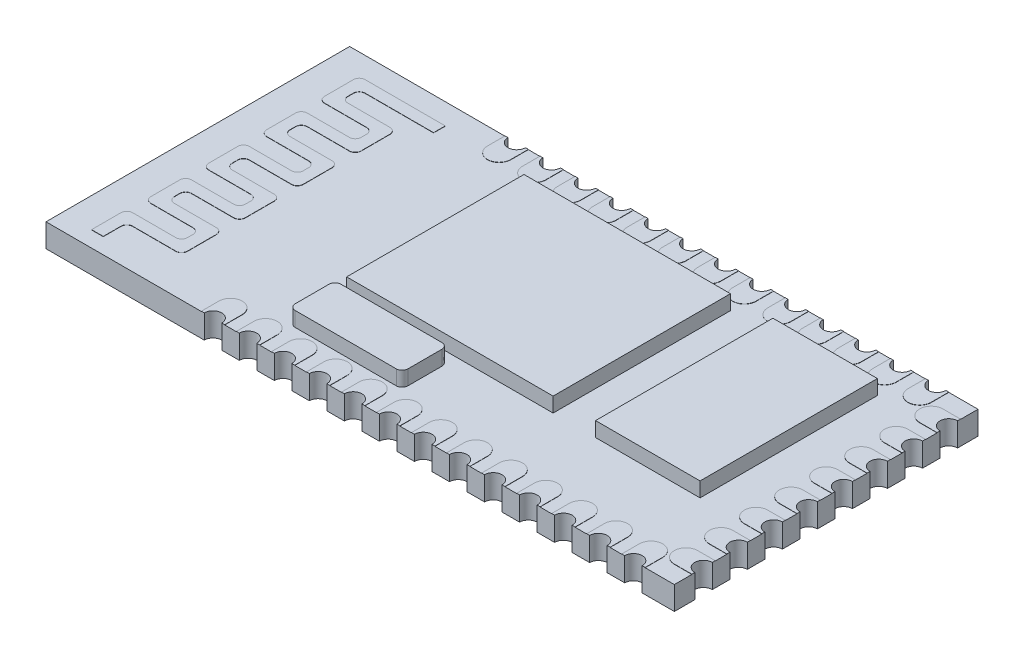
SolidWorks part; units mm, degrees
ref_plane "Front Plane" through (0, 0, 0) normal (0, 0, 1) x (1, 0, 0)
ref_plane "Top Plane" through (0, 0, 0) normal (0, 1, 0) x (1, 0, 0)
ref_plane "Right Plane" through (0, 0, 0) normal (1, 0, 0) x (0, 0, -1)
sketch "Sketch1" plane through (0, 0, 0) normal (0, 1, 0) x (1, 0, 0)
  line L1 (0, 0) -> (26.9, 0)
  line L2 (0, 0) -> (0, 13)
  line L3 (0, 13) -> (26.9, 13)
  line L4 (26.9, 0) -> (26.9, 13)
  dimension "D1" = 13
  dimension "D2" = 26.9
extrude "Boss-Extrude1" add sketch "Sketch1" along normal blind 1
sketch "Sketch2" plane through (0, 1, 0) normal (0, 1, 0) x (1, 0, 0)
  line L1 (24.2376, 11.3557) -> (19.7636, 11.3557)
  line L2 (24.2376, 11.3557) -> (24.2376, 3.7634)
  line L3 (24.2376, 3.7634) -> (19.7636, 3.7634)
  line L4 (19.7636, 11.3557) -> (19.7636, 3.7634)
  line L5 (9.1073, 11.3557) -> (17.9469, 11.3557)
  line L6 (9.1073, 11.3557) -> (9.1073, 3.7634)
  line L7 (9.1073, 3.7634) -> (17.9469, 3.7634)
  line L8 (17.9469, 11.3557) -> (17.9469, 3.7634)
extrude "Boss-Extrude2" add sketch "Sketch2" along normal blind 0.63
sketch "Sketch3" plane through (0, 1, 0) normal (0, 1, 0) x (1, 0, 0)
  line L0 (5.0017, 11.8414) -> (1.5699, 11.8414) construction
  line L1 (1.5699, 11.8414) -> (1.5699, 10.6027) construction
  line L2 (1.5699, 10.6027) -> (3.8747, 10.6027) construction
  line L3 (3.8747, 10.6027) -> (3.8747, 9.364) construction
  line L4 (3.8747, 9.364) -> (1.5699, 9.364) construction
  line L5 (1.5699, 9.364) -> (1.5699, 8.1252) construction
  line L6 (1.5699, 8.1252) -> (3.8747, 8.1252) construction
  line L7 (3.8747, 8.1252) -> (3.8747, 6.8865) construction
  line L8 (3.8747, 6.8865) -> (1.5699, 6.8865) construction
  line L9 (1.5699, 6.8865) -> (1.5699, 5.6478) construction
  line L10 (1.5699, 5.6478) -> (3.8747, 5.6478) construction
  line L11 (3.8747, 5.6478) -> (3.8747, 4.4091) construction
  line L12 (3.8747, 4.4091) -> (1.5699, 4.4091) construction
  line L13 (1.5699, 4.4091) -> (1.5699, 3.1704) construction
  line L14 (1.5699, 3.1704) -> (3.8747, 3.1704) construction
  line L15 (3.8747, 3.1704) -> (3.8747, 1.9317) construction
  line L16 (3.8747, 1.9317) -> (1.527, 1.9317) construction
  line L17 (1.527, 1.4451) -> (1.527, 0.1872) construction
  line L18 (5.0017, 12.0914) -> (1.5699, 12.0914)
  line L19 (1.3199, 11.8414) -> (1.3199, 10.6027)
  line L20 (1.5699, 10.3527) -> (3.3747, 10.3527)
  line L21 (3.6247, 10.1027) -> (3.6247, 9.864)
  line L22 (3.3747, 9.614) -> (1.5699, 9.614)
  line L23 (1.3199, 9.364) -> (1.3199, 8.1252)
  line L24 (1.5699, 7.8752) -> (3.3747, 7.8752)
  line L25 (3.6247, 7.6252) -> (3.6247, 7.3865)
  line L26 (3.3747, 7.1365) -> (1.5699, 7.1365)
  line L27 (1.3199, 6.8865) -> (1.3199, 5.6478)
  line L28 (1.5699, 5.3978) -> (3.3747, 5.3978)
  line L29 (3.6247, 5.1478) -> (3.6247, 4.9091)
  line L30 (3.3747, 4.6591) -> (1.5699, 4.6591)
  line L31 (1.3199, 4.4091) -> (1.3199, 3.1704)
  line L32 (1.5699, 2.9204) -> (3.3747, 2.9204)
  line L33 (3.6247, 2.6704) -> (3.6247, 2.4317)
  line L34 (3.3747, 2.1817) -> (1.527, 2.1817)
  line L35 (1.277, 1.9317) -> (1.277, 0.6739)
  line L36 (5.0017, 11.5914) -> (2.0699, 11.5914)
  line L37 (1.8199, 11.3414) -> (1.8199, 11.1027)
  line L38 (2.0699, 10.8527) -> (3.8747, 10.8527)
  line L39 (4.1247, 10.6027) -> (4.1247, 9.364)
  line L40 (3.8747, 9.114) -> (2.0699, 9.114)
  line L41 (1.8199, 8.864) -> (1.8199, 8.6252)
  line L42 (2.0699, 8.3752) -> (3.8747, 8.3752)
  line L43 (4.1247, 8.1252) -> (4.1247, 6.8865)
  line L44 (3.8747, 6.6365) -> (2.0699, 6.6365)
  line L45 (1.8199, 6.3865) -> (1.8199, 6.1478)
  line L46 (2.0699, 5.8978) -> (3.8747, 5.8978)
  line L47 (4.1247, 5.6478) -> (4.1247, 4.4091)
  line L48 (3.8747, 4.1591) -> (2.0699, 4.1591)
  line L49 (1.8199, 3.9091) -> (1.8199, 3.6704)
  line L50 (2.0699, 3.4204) -> (3.8747, 3.4204)
  line L51 (4.1247, 3.1704) -> (4.1247, 1.9317)
  line L52 (3.8747, 1.6817) -> (2.027, 1.6817)
  line L53 (1.777, 1.4317) -> (1.777, 0.6739)
  line L54 (5.0017, 12.0914) -> (5.0017, 11.5914)
  line L55 (1.777, 0.6739) -> (1.277, 0.6739)
  arc A0 (1.5699, 12.0914) -> (1.3199, 11.8414) centre (1.5699, 11.8414) ccw
  arc A1 (2.0699, 11.5914) -> (1.8199, 11.3414) centre (2.0699, 11.3414) ccw
  arc A2 (1.8199, 11.1027) -> (2.0699, 10.8527) centre (2.0699, 11.1027) ccw
  arc A3 (1.3199, 10.6027) -> (1.5699, 10.3527) centre (1.5699, 10.6027) ccw
  arc A4 (3.8747, 10.8527) -> (4.1247, 10.6027) centre (3.8747, 10.6027) cw
  arc A5 (3.3747, 10.3527) -> (3.6247, 10.1027) centre (3.3747, 10.1027) cw
  arc A6 (3.6247, 9.864) -> (3.3747, 9.614) centre (3.3747, 9.864) cw
  arc A7 (4.1247, 9.364) -> (3.8747, 9.114) centre (3.8747, 9.364) cw
  arc A8 (2.0699, 9.114) -> (1.8199, 8.864) centre (2.0699, 8.864) ccw
  arc A9 (1.5699, 9.614) -> (1.3199, 9.364) centre (1.5699, 9.364) ccw
  arc A10 (1.8199, 8.6252) -> (2.0699, 8.3752) centre (2.0699, 8.6252) ccw
  arc A11 (1.3199, 8.1252) -> (1.5699, 7.8752) centre (1.5699, 8.1252) ccw
  arc A12 (3.3747, 7.8752) -> (3.6247, 7.6252) centre (3.3747, 7.6252) cw
  arc A13 (3.8747, 8.3752) -> (4.1247, 8.1252) centre (3.8747, 8.1252) cw
  arc A14 (4.1247, 6.8865) -> (3.8747, 6.6365) centre (3.8747, 6.8865) cw
  arc A15 (3.6247, 7.3865) -> (3.3747, 7.1365) centre (3.3747, 7.3865) cw
  arc A16 (1.5699, 7.1365) -> (1.3199, 6.8865) centre (1.5699, 6.8865) ccw
  arc A17 (2.0699, 6.6365) -> (1.8199, 6.3865) centre (2.0699, 6.3865) ccw
  arc A18 (1.8199, 6.1478) -> (2.0699, 5.8978) centre (2.0699, 6.1478) ccw
  arc A19 (1.3199, 5.6478) -> (1.5699, 5.3978) centre (1.5699, 5.6478) ccw
  arc A20 (3.3747, 5.3978) -> (3.6247, 5.1478) centre (3.3747, 5.1478) cw
  arc A21 (3.8747, 5.8978) -> (4.1247, 5.6478) centre (3.8747, 5.6478) cw
  arc A22 (4.1247, 4.4091) -> (3.8747, 4.1591) centre (3.8747, 4.4091) cw
  arc A23 (3.6247, 4.9091) -> (3.3747, 4.6591) centre (3.3747, 4.9091) cw
  arc A24 (1.5699, 4.6591) -> (1.3199, 4.4091) centre (1.5699, 4.4091) ccw
  arc A25 (2.0699, 4.1591) -> (1.8199, 3.9091) centre (2.0699, 3.9091) ccw
  arc A26 (1.8199, 3.6704) -> (2.0699, 3.4204) centre (2.0699, 3.6704) ccw
  arc A27 (1.3199, 3.1704) -> (1.5699, 2.9204) centre (1.5699, 3.1704) ccw
  arc A28 (2.027, 1.6817) -> (1.777, 1.4317) centre (2.027, 1.4317) ccw
  arc A29 (1.527, 2.1817) -> (1.277, 1.9317) centre (1.527, 1.9317) ccw
  arc A30 (3.8747, 3.4204) -> (4.1247, 3.1704) centre (3.8747, 3.1704) cw
  arc A31 (3.3747, 2.9204) -> (3.6247, 2.6704) centre (3.3747, 2.6704) cw
  arc A32 (3.6247, 2.4317) -> (3.3747, 2.1817) centre (3.3747, 2.4317) cw
  arc A33 (4.1247, 1.9317) -> (3.8747, 1.6817) centre (3.8747, 1.9317) cw
  dimension "D1" = 0.25
extrude "Boss-Extrude3" add sketch "Sketch3" along normal blind 0.01
sketch "Sketch4" plane through (0, 1, 0) normal (0, 1, 0) x (1, 0, 0)
  line L1 (9.2531, 3.3678) -> (13.5796, 3.3678)
  line L2 (9.0031, 3.1178) -> (9.0031, 1.6655)
  line L3 (9.2531, 1.4155) -> (13.5796, 1.4155)
  line L4 (13.8296, 3.1178) -> (13.8296, 1.6655)
  arc A0 (13.5796, 1.4155) -> (13.8296, 1.6655) centre (13.5796, 1.6655) ccw
  arc A1 (9.2531, 3.3678) -> (9.0031, 3.1178) centre (9.2531, 3.1178) ccw
  arc A2 (9.0031, 1.6655) -> (9.2531, 1.4155) centre (9.2531, 1.6655) ccw
  arc A3 (13.5796, 3.3678) -> (13.8296, 3.1178) centre (13.5796, 3.1178) cw
  dimension "D1" = 0.25
extrude "Boss-Extrude4" add sketch "Sketch4" along normal up to surface (0.63 mm away) up to face at (13.5271, 1.63, -7.5596)
sketch "Sketch5" plane through (0, 1, 0) normal (0, 1, 0) x (1, 0, 0)
  line L0 (0, 6.5) -> (26.9, 6.5) construction
  line L1 (0, 13) -> (0, 0) construction
  line L2 (26.9, 0) -> (26.9, 13) construction
  line L3 (26.15, 11.75) -> (28.15, 11.75) construction
  line L4 (26.15, 12.25) -> (28.15, 12.25)
  line L5 (26.15, 11.25) -> (28.15, 11.25)
  line L7 (26.15, 10.25) -> (28.15, 10.25) construction
  line L8 (26.15, 10.75) -> (28.15, 10.75)
  line L9 (26.15, 9.75) -> (28.15, 9.75)
  line L10 (26.15, 8.75) -> (28.15, 8.75) construction
  line L11 (26.15, 9.25) -> (28.15, 9.25)
  line L12 (26.15, 8.25) -> (28.15, 8.25)
  line L13 (26.15, 7.25) -> (28.15, 7.25) construction
  line L14 (26.15, 7.75) -> (28.15, 7.75)
  line L15 (26.15, 6.75) -> (28.15, 6.75)
  line L16 (26.15, 5.75) -> (28.15, 5.75) construction
  line L17 (26.15, 6.25) -> (28.15, 6.25)
  line L18 (26.15, 5.25) -> (28.15, 5.25)
  line L19 (26.15, 4.25) -> (28.15, 4.25) construction
  line L20 (26.15, 4.75) -> (28.15, 4.75)
  line L21 (26.15, 3.75) -> (28.15, 3.75)
  line L22 (26.15, 2.75) -> (28.15, 2.75) construction
  line L23 (26.15, 3.25) -> (28.15, 3.25)
  line L24 (26.15, 2.25) -> (28.15, 2.25)
  line L25 (26.15, 1.25) -> (28.15, 1.25) construction
  line L26 (26.15, 1.75) -> (28.15, 1.75)
  line L27 (26.15, 0.75) -> (28.15, 0.75)
  line L30 (25.15, 12.25) -> (25.15, 14.25) construction
  line L31 (24.65, 12.25) -> (24.65, 14.25)
  line L32 (25.65, 12.25) -> (25.65, 14.25)
  line L33 (26.9, 13) -> (0, 13) construction
  line L34 (23.65, 12.25) -> (23.65, 14.25) construction
  line L35 (23.15, 12.25) -> (23.15, 14.25)
  line L36 (24.15, 12.25) -> (24.15, 14.25)
  line L37 (22.15, 12.25) -> (22.15, 14.25) construction
  line L38 (21.65, 12.25) -> (21.65, 14.25)
  line L39 (22.65, 12.25) -> (22.65, 14.25)
  line L40 (20.65, 12.25) -> (20.65, 14.25) construction
  line L41 (20.15, 12.25) -> (20.15, 14.25)
  line L42 (21.15, 12.25) -> (21.15, 14.25)
  line L43 (19.15, 12.25) -> (19.15, 14.25) construction
  line L44 (18.65, 12.25) -> (18.65, 14.25)
  line L45 (19.65, 12.25) -> (19.65, 14.25)
  line L46 (17.65, 12.25) -> (17.65, 14.25) construction
  line L47 (17.15, 12.25) -> (17.15, 14.25)
  line L48 (18.15, 12.25) -> (18.15, 14.25)
  line L49 (16.15, 12.25) -> (16.15, 14.25) construction
  line L50 (15.65, 12.25) -> (15.65, 14.25)
  line L51 (16.65, 12.25) -> (16.65, 14.25)
  line L52 (14.65, 12.25) -> (14.65, 14.25) construction
  line L53 (14.15, 12.25) -> (14.15, 14.25)
  line L54 (15.15, 12.25) -> (15.15, 14.25)
  line L55 (13.15, 12.25) -> (13.15, 14.25) construction
  line L56 (12.65, 12.25) -> (12.65, 14.25)
  line L57 (13.65, 12.25) -> (13.65, 14.25)
  line L58 (11.65, 12.25) -> (11.65, 14.25) construction
  line L59 (11.15, 12.25) -> (11.15, 14.25)
  line L60 (12.15, 12.25) -> (12.15, 14.25)
  line L61 (10.15, 12.25) -> (10.15, 14.25) construction
  line L62 (9.65, 12.25) -> (9.65, 14.25)
  line L63 (10.65, 12.25) -> (10.65, 14.25)
  line L64 (8.65, 12.25) -> (8.65, 14.25) construction
  line L65 (8.15, 12.25) -> (8.15, 14.25)
  line L66 (9.15, 12.25) -> (9.15, 14.25)
  line L67 (7.15, 12.25) -> (7.15, 14.25) construction
  line L68 (6.65, 12.25) -> (6.65, 14.25)
  line L69 (7.65, 12.25) -> (7.65, 14.25)
  line L70 (25.15, 0.75) -> (25.15, -1.25) construction
  line L71 (24.65, 0.75) -> (24.65, -1.25)
  line L72 (25.65, 0.75) -> (25.65, -1.25)
  line L73 (23.65, 0.75) -> (23.65, -1.25) construction
  line L74 (23.15, 0.75) -> (23.15, -1.25)
  line L75 (24.15, 0.75) -> (24.15, -1.25)
  line L76 (22.15, 0.75) -> (22.15, -1.25) construction
  line L77 (21.65, 0.75) -> (21.65, -1.25)
  line L78 (22.65, 0.75) -> (22.65, -1.25)
  line L79 (20.65, 0.75) -> (20.65, -1.25) construction
  line L80 (20.15, 0.75) -> (20.15, -1.25)
  line L81 (21.15, 0.75) -> (21.15, -1.25)
  line L82 (19.15, 0.75) -> (19.15, -1.25) construction
  line L83 (18.65, 0.75) -> (18.65, -1.25)
  line L84 (19.65, 0.75) -> (19.65, -1.25)
  line L85 (17.65, 0.75) -> (17.65, -1.25) construction
  line L86 (17.15, 0.75) -> (17.15, -1.25)
  line L87 (18.15, 0.75) -> (18.15, -1.25)
  line L88 (16.15, 0.75) -> (16.15, -1.25) construction
  line L89 (15.65, 0.75) -> (15.65, -1.25)
  line L90 (16.65, 0.75) -> (16.65, -1.25)
  line L91 (14.65, 0.75) -> (14.65, -1.25) construction
  line L92 (14.15, 0.75) -> (14.15, -1.25)
  line L93 (15.15, 0.75) -> (15.15, -1.25)
  line L94 (13.15, 0.75) -> (13.15, -1.25) construction
  line L95 (12.65, 0.75) -> (12.65, -1.25)
  line L96 (13.65, 0.75) -> (13.65, -1.25)
  line L97 (11.65, 0.75) -> (11.65, -1.25) construction
  line L98 (11.15, 0.75) -> (11.15, -1.25)
  line L99 (12.15, 0.75) -> (12.15, -1.25)
  line L100 (10.15, 0.75) -> (10.15, -1.25) construction
  line L101 (9.65, 0.75) -> (9.65, -1.25)
  line L102 (10.65, 0.75) -> (10.65, -1.25)
  line L103 (8.65, 0.75) -> (8.65, -1.25) construction
  line L104 (8.15, 0.75) -> (8.15, -1.25)
  line L105 (9.15, 0.75) -> (9.15, -1.25)
  line L106 (7.15, 0.75) -> (7.15, -1.25) construction
  line L107 (6.65, 0.75) -> (6.65, -1.25)
  line L108 (7.65, 0.75) -> (7.65, -1.25)
  arc A0 (26.15, 12.25) -> (26.15, 11.25) centre (26.15, 11.75) ccw
  arc A1 (28.15, 11.25) -> (28.15, 12.25) centre (28.15, 11.75) ccw
  arc A2 (26.15, 10.75) -> (26.15, 9.75) centre (26.15, 10.25) ccw
  arc A3 (28.15, 9.75) -> (28.15, 10.75) centre (28.15, 10.25) ccw
  arc A4 (26.15, 9.25) -> (26.15, 8.25) centre (26.15, 8.75) ccw
  arc A5 (28.15, 8.25) -> (28.15, 9.25) centre (28.15, 8.75) ccw
  arc A6 (26.15, 7.75) -> (26.15, 6.75) centre (26.15, 7.25) ccw
  arc A7 (28.15, 6.75) -> (28.15, 7.75) centre (28.15, 7.25) ccw
  arc A8 (26.15, 6.25) -> (26.15, 5.25) centre (26.15, 5.75) ccw
  arc A9 (28.15, 5.25) -> (28.15, 6.25) centre (28.15, 5.75) ccw
  arc A10 (26.15, 4.75) -> (26.15, 3.75) centre (26.15, 4.25) ccw
  arc A11 (28.15, 3.75) -> (28.15, 4.75) centre (28.15, 4.25) ccw
  arc A12 (26.15, 3.25) -> (26.15, 2.25) centre (26.15, 2.75) ccw
  arc A13 (28.15, 2.25) -> (28.15, 3.25) centre (28.15, 2.75) ccw
  arc A14 (26.15, 1.75) -> (26.15, 0.75) centre (26.15, 1.25) ccw
  arc A15 (28.15, 0.75) -> (28.15, 1.75) centre (28.15, 1.25) ccw
  arc A16 (24.65, 12.25) -> (25.65, 12.25) centre (25.15, 12.25) ccw
  arc A17 (25.65, 14.25) -> (24.65, 14.25) centre (25.15, 14.25) ccw
  arc A18 (23.15, 12.25) -> (24.15, 12.25) centre (23.65, 12.25) ccw
  arc A19 (24.15, 14.25) -> (23.15, 14.25) centre (23.65, 14.25) ccw
  arc A20 (21.65, 12.25) -> (22.65, 12.25) centre (22.15, 12.25) ccw
  arc A21 (22.65, 14.25) -> (21.65, 14.25) centre (22.15, 14.25) ccw
  arc A22 (20.15, 12.25) -> (21.15, 12.25) centre (20.65, 12.25) ccw
  arc A23 (21.15, 14.25) -> (20.15, 14.25) centre (20.65, 14.25) ccw
  arc A24 (18.65, 12.25) -> (19.65, 12.25) centre (19.15, 12.25) ccw
  arc A25 (19.65, 14.25) -> (18.65, 14.25) centre (19.15, 14.25) ccw
  arc A26 (17.15, 12.25) -> (18.15, 12.25) centre (17.65, 12.25) ccw
  arc A27 (18.15, 14.25) -> (17.15, 14.25) centre (17.65, 14.25) ccw
  arc A28 (15.65, 12.25) -> (16.65, 12.25) centre (16.15, 12.25) ccw
  arc A29 (16.65, 14.25) -> (15.65, 14.25) centre (16.15, 14.25) ccw
  arc A30 (14.15, 12.25) -> (15.15, 12.25) centre (14.65, 12.25) ccw
  arc A31 (15.15, 14.25) -> (14.15, 14.25) centre (14.65, 14.25) ccw
  arc A32 (12.65, 12.25) -> (13.65, 12.25) centre (13.15, 12.25) ccw
  arc A33 (13.65, 14.25) -> (12.65, 14.25) centre (13.15, 14.25) ccw
  arc A34 (11.15, 12.25) -> (12.15, 12.25) centre (11.65, 12.25) ccw
  arc A35 (12.15, 14.25) -> (11.15, 14.25) centre (11.65, 14.25) ccw
  arc A36 (9.65, 12.25) -> (10.65, 12.25) centre (10.15, 12.25) ccw
  arc A37 (10.65, 14.25) -> (9.65, 14.25) centre (10.15, 14.25) ccw
  arc A38 (8.15, 12.25) -> (9.15, 12.25) centre (8.65, 12.25) ccw
  arc A39 (9.15, 14.25) -> (8.15, 14.25) centre (8.65, 14.25) ccw
  arc A40 (6.65, 12.25) -> (7.65, 12.25) centre (7.15, 12.25) ccw
  arc A41 (7.65, 14.25) -> (6.65, 14.25) centre (7.15, 14.25) ccw
  arc A42 (24.65, 0.75) -> (25.65, 0.75) centre (25.15, 0.75) cw
  arc A43 (25.65, -1.25) -> (24.65, -1.25) centre (25.15, -1.25) cw
  arc A44 (23.15, 0.75) -> (24.15, 0.75) centre (23.65, 0.75) cw
  arc A45 (24.15, -1.25) -> (23.15, -1.25) centre (23.65, -1.25) cw
  arc A46 (21.65, 0.75) -> (22.65, 0.75) centre (22.15, 0.75) cw
  arc A47 (22.65, -1.25) -> (21.65, -1.25) centre (22.15, -1.25) cw
  arc A48 (20.15, 0.75) -> (21.15, 0.75) centre (20.65, 0.75) cw
  arc A49 (21.15, -1.25) -> (20.15, -1.25) centre (20.65, -1.25) cw
  arc A50 (18.65, 0.75) -> (19.65, 0.75) centre (19.15, 0.75) cw
  arc A51 (19.65, -1.25) -> (18.65, -1.25) centre (19.15, -1.25) cw
  arc A52 (17.15, 0.75) -> (18.15, 0.75) centre (17.65, 0.75) cw
  arc A53 (18.15, -1.25) -> (17.15, -1.25) centre (17.65, -1.25) cw
  arc A54 (15.65, 0.75) -> (16.65, 0.75) centre (16.15, 0.75) cw
  arc A55 (16.65, -1.25) -> (15.65, -1.25) centre (16.15, -1.25) cw
  arc A56 (14.15, 0.75) -> (15.15, 0.75) centre (14.65, 0.75) cw
  arc A57 (15.15, -1.25) -> (14.15, -1.25) centre (14.65, -1.25) cw
  arc A58 (12.65, 0.75) -> (13.65, 0.75) centre (13.15, 0.75) cw
  arc A59 (13.65, -1.25) -> (12.65, -1.25) centre (13.15, -1.25) cw
  arc A60 (11.15, 0.75) -> (12.15, 0.75) centre (11.65, 0.75) cw
  arc A61 (12.15, -1.25) -> (11.15, -1.25) centre (11.65, -1.25) cw
  arc A62 (9.65, 0.75) -> (10.65, 0.75) centre (10.15, 0.75) cw
  arc A63 (10.65, -1.25) -> (9.65, -1.25) centre (10.15, -1.25) cw
  arc A64 (8.15, 0.75) -> (9.15, 0.75) centre (8.65, 0.75) cw
  arc A65 (9.15, -1.25) -> (8.15, -1.25) centre (8.65, -1.25) cw
  arc A66 (6.65, 0.75) -> (7.65, 0.75) centre (7.15, 0.75) cw
  arc A67 (7.65, -1.25) -> (6.65, -1.25) centre (7.15, -1.25) cw
  point P8 (27.15, 11.75)
  point P18 (27.15, 10.25)
  point P25 (27.15, 8.75)
  point P32 (27.15, 7.25)
  point P39 (27.15, 5.75)
  point P46 (27.15, 4.25)
  point P53 (27.15, 2.75)
  point P60 (27.15, 1.25)
  point P66 (25.15, 13.25)
  point P75 (23.65, 13.25)
  point P82 (22.15, 13.25)
  point P89 (20.65, 13.25)
  point P96 (19.15, 13.25)
  point P103 (17.65, 13.25)
  point P110 (16.15, 13.25)
  point P117 (14.65, 13.25)
  point P124 (13.15, 13.25)
  point P131 (11.65, 13.25)
  point P138 (10.15, 13.25)
  point P145 (8.65, 13.25)
  point P152 (7.15, 13.25)
  point P157 (25.15, -0.25)
  point P164 (23.65, -0.25)
  point P171 (22.15, -0.25)
  point P178 (20.65, -0.25)
  point P185 (19.15, -0.25)
  point P192 (17.65, -0.25)
  point P199 (16.15, -0.25)
  point P206 (14.65, -0.25)
  point P213 (13.15, -0.25)
  point P220 (11.65, -0.25)
  point P227 (10.15, -0.25)
  point P234 (8.65, -0.25)
  point P241 (7.15, -0.25)
  dimension "D4" = 0.75
  dimension "D1" = 1
  dimension "D2" = 1.25
  dimension "D3" = 2
  dimension "D6" = 2
  dimension "D7" = 1
  dimension "D8" = 0.75
  dimension "D9" = 1.75
  dimension "D5" = 8
  dimension "D10" = 13
extrude "Boss-Extrude5" add sketch "Sketch5" along normal blind 0.01
sketch "Sketch7" plane through (0, 1.01, 0) normal (0, 1, 0) x (1, 0, 0)
  line L1 (6.65, 13) -> (26.9, 13)
  line L2 (6.65, 13) -> (6.65, 15.0045)
  line L3 (6.65, 15.0045) -> (26.9, 15.0045)
  line L5 (26.9, 15.0045) -> (29.0707, 15.0045)
  line L6 (26.9, 15.0045) -> (26.9, 0)
  line L8 (29.0707, 15.0045) -> (29.0707, 0)
  line L9 (29.0707, 0) -> (6.65, 0)
  line L10 (29.0707, 0) -> (29.0707, -1.8715)
  line L11 (29.0707, -1.8715) -> (6.65, -1.8715)
  line L12 (6.65, 0) -> (6.65, -1.8715)
  line M2 (7.65, 12.25) -> (7.65, 14.25)
  arc M3 (7.65, 14.25) -> (6.65, 14.25) centre (7.15, 14.25) ccw
  line M4 (6.65, 14.25) -> (6.65, 12.25)
extrude "Cut-Extrude1" cut sketch "Sketch7" against normal through all contours L6 L3 L2 L1 M3 M2 | L9 L8 L5 L6 | L1 M4 M2 M3 | L9 L12 L11 L10
sketch "Sketch8" plane through (0, 1.01, 0) normal (0, 1, 0) x (1, 0, 0)
  line L0 (6.65, 13) -> (7.65, 13) construction
  line L1 (6.65, 0) -> (7.65, 0) construction
  circle A0 centre (7.15, 13) radius 0.375
  circle A1 centre (7.15, 0) radius 0.375
  dimension "D1" = 0.75
  dimension "D2" = 0.75
extrude "Cut-Extrude2" cut sketch "Sketch8" against normal through all
pattern_linear "LPattern1" count 13 spacing 1.5 along (1, 0, 0) of "Cut-Extrude2"
sketch "Sketch9" plane through (0, 1.01, 0) normal (0, 1, 0) x (1, 0, 0)
  line L0 (26.9, 12.25) -> (26.9, 11.25) construction
  circle A0 centre (26.9, 11.75) radius 0.375
  dimension "D1" = 0.75
extrude "Cut-Extrude3" cut sketch "Sketch9" against normal through all
pattern_linear "LPattern2" count 8 spacing 1.5 along (0, 0, 1) of "Cut-Extrude3"
scale "Scale1" bodies to scale 114 scale about centroid uniform scaling yes scale factor 1.769
